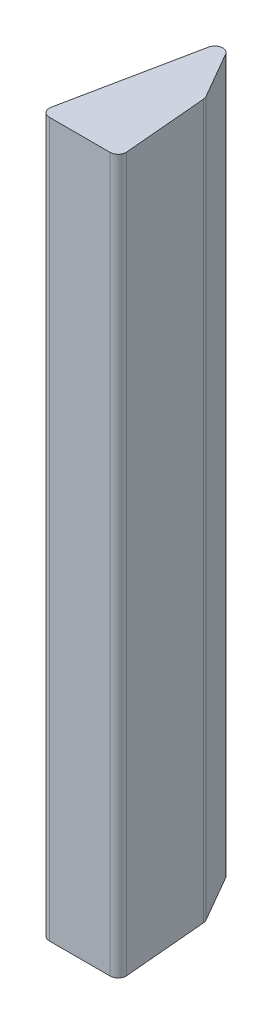
SolidWorks part; units mm, degrees
ref_plane "Спереди" through (0, 0, 0) normal (0, 0, 1) x (1, 0, 0)
ref_plane "Сверху" through (0, 0, 0) normal (0, 1, 0) x (1, 0, 0)
ref_plane "Справа" through (0, 0, 0) normal (1, 0, 0) x (0, 0, -1)
sketch "Эскиз1" plane through (0, 0, 0) normal (0, 1, 0) x (1, 0, 0)
  line L0 (-43.879, 0) -> (-5.4565, 0)
  line L1 (-0.4756, 5.4358) -> (-5.1327, 58.6674)
  line L2 (-5.7836, 60.7316) -> (-22.7293, 90.0826)
  line L3 (-31.9589, 88.5804) -> (-48.7784, 5.9979)
  arc A3 (-22.7293, 90.0826) -> (-31.9589, 88.5804) centre (-27.0595, 87.5826) ccw
  arc A4 (-43.879, 0) -> (-48.7784, 5.9979) centre (-43.879, 5) cw
  arc A5 (-0.4756, 5.4358) -> (-5.4565, 0) centre (-5.4565, 5) cw
  arc A6 (-5.1327, 58.6674) -> (-5.7836, 60.7316) centre (-10.1137, 58.2316) ccw
  point P0 (17.9839, 57.2414)
  point P6 (-50, 0)
  point P9 (0, 0)
  point P12 (-5.2293, 59.7717)
  point P15 (0, 0)
  point P18 (-5.2293, 59.7717)
  dimension "D1" = 85
  dimension "D2" = 5
  dimension "D7" = 5
  dimension "D3" = 155
  dimension "D4" = 60
  dimension "D5" = 50
  dimension "D6" = 35
other "Выровнять группу1"
extrude "Бобышка-Вытянуть1" add sketch "Эскиз1" along normal blind 450
